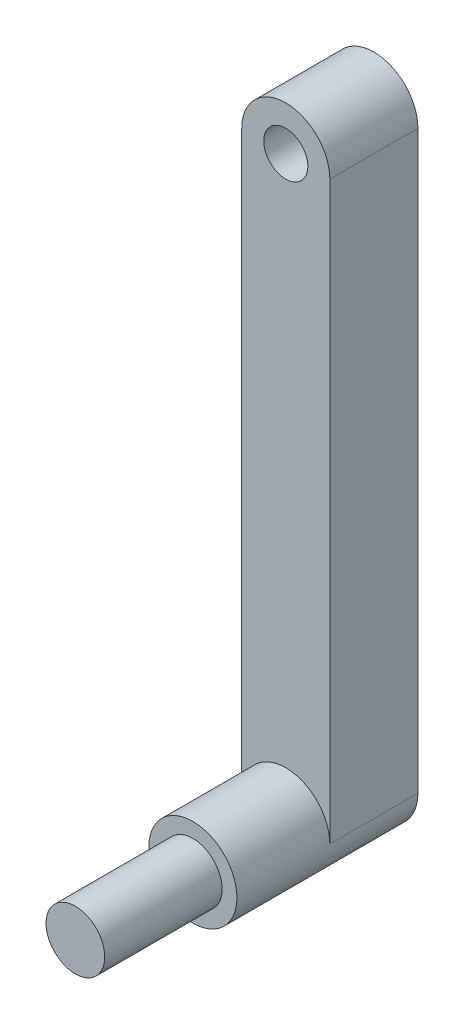
SolidWorks part; units mm, degrees
ref_plane "Front Plane" through (0, 0, 0) normal (0, 0, 1) x (1, 0, 0)
ref_plane "Top Plane" through (0, 0, 0) normal (0, 1, 0) x (1, 0, 0)
ref_plane "Right Plane" through (0, 0, 0) normal (1, 0, 0) x (0, 0, -1)
sketch "sketch1_link3" plane through (0, 0, 0) normal (0, 0, 1) x (1, 0, 0)
  circle A0 centre (0, 0) radius 20
  dimension "D1" = 40
extrude "Boss-Extrude1" add sketch "sketch1_link3" along normal mid plane 80
sketch "sketch2_link3" plane through (0, 0, -40) normal (0, 0, -1) x (-1, 0, 0)
  circle A0 centre (0, 0) radius 30
  dimension "D1" = 60
extrude "Boss-Extrude2" add sketch "sketch2_link3" along normal blind 63.3
sketch "sketch3_link3" plane through (0, 0, -103.3) normal (0, 0, -1) x (-1, 0, 0)
  line L0 (-30, 0) -> (-30, 392.2)
  line L1 (30, 0) -> (30, 392.2)
  arc A0 (30, 0) -> (-30, 0) centre (0, 0) cw
  arc A1 (-30, 392.2) -> (30, 392.2) centre (0, 392.2) cw
  circle A2 centre (0, 392.2) radius 15
  dimension "D1" = 30
  dimension "D3" = 30
  dimension "D2" = 392.2
extrude "Boss-Extrude3" add sketch "sketch3_link3" along normal blind 60
sketch "Sketch1" plane through (0, 0, -163.3) normal (0, 0, -1) x (-1, 0, 0)
  line L0 (10, -28.2843) -> (10, 420.4843) construction
  arc A0 (-30, 0) -> (30, 0) centre (0, 0) ccw construction
  arc A2 (30, 392.2) -> (-30, 392.2) centre (0, 392.2) ccw construction
  text T0 "JUSTBOT" font "D-DIN Exp" height in points 72
  dimension "D1" = 40
extrude "Boss-Extrude4" add sketch "Sketch1" along normal blind 0.1
